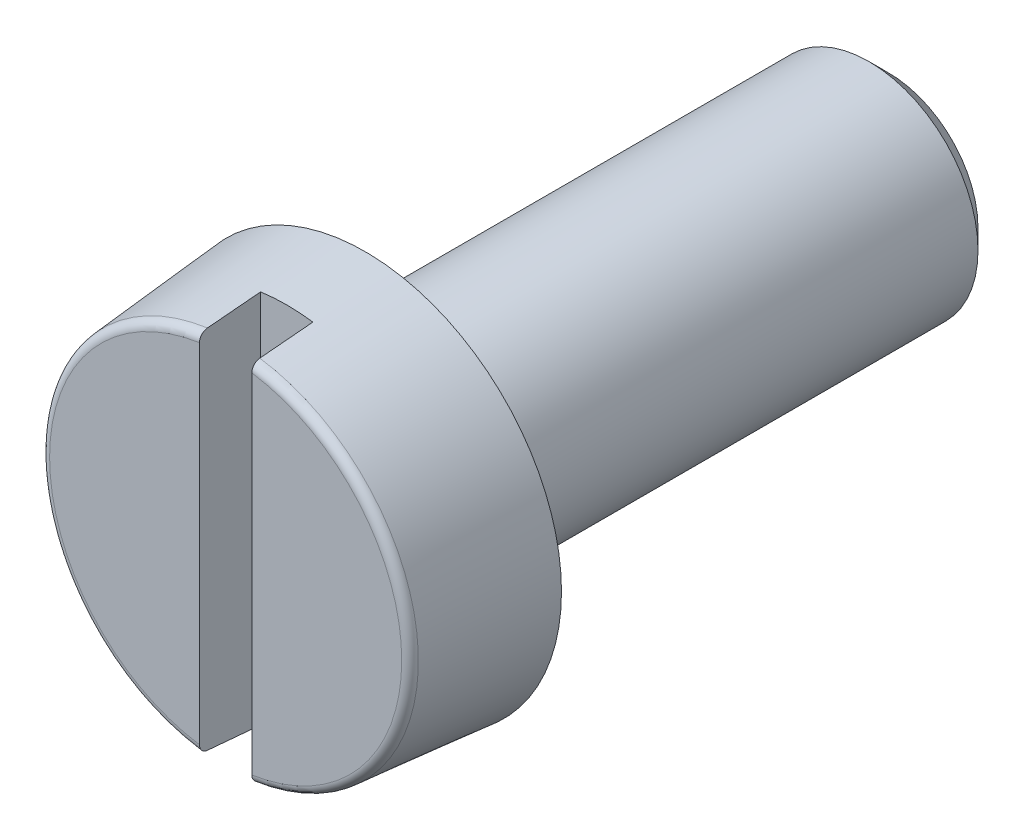
SolidWorks part; units mm, degrees
ref_plane "Front Plane" through (0, 0, 0) normal (0, 0, 1) x (1, 0, 0)
ref_plane "Top Plane" through (0, 0, 0) normal (0, 1, 0) x (1, 0, 0)
ref_plane "Right Plane" through (0, 0, 0) normal (1, 0, 0) x (0, 0, -1)
sketch "Sketch1" plane through (0, 0, 0) normal (1, 0, 0) x (0, 0, -1)
  line L0 (0, 0) -> (18.1531, 0) construction
  line L3 (0, 0) -> (0, 2.0184)
  line L4 (0.0913, 2.118) -> (1.6, 2.25)
  line L5 (1.6, 2.25) -> (1.6, 1.35)
  line L6 (1.7, 1.25) -> (7.375, 1.25)
  line L7 (7.375, 1.25) -> (7.6, 1.025)
  line L8 (7.6, 1.025) -> (7.6, 0)
  line L9 (7.6, 0) -> (0, 0)
  arc A0 (0, 2.0184) -> (0.0913, 2.118) centre (0.1, 2.0184) cw
  arc A1 (1.6, 1.35) -> (1.7, 1.25) centre (1.7, 1.35) ccw
  dimension "a" = 0.1
  dimension "R" = 0.1
  dimension "D1" = 45
  dimension "Dk" = 4.5
  dimension "K" = 1.6
  dimension "Hole1" = 2.5
  dimension "Hole2" = 2.05
  dimension "Length" = 6
  dimension "D8" = 85
revolve "Revolve1" add sketch "Sketch1" angle 360 about L0
cosmetic thread "Cosmetic Thread1" parameters "D1"=5.1, "D2"=2.5
sketch "Sketch2" plane through (0, 0, 0) normal (0, 0, 1) x (1, 0, 0)
  line L0 (0, 0) -> (0, 2.25) construction
  line L1 (-0.3, 2.25) -> (0.3, 2.25)
  line L2 (0.3, 2.25) -> (0.3, -2.25)
  line L3 (-0.3, 2.25) -> (-0.3, -2.25)
  line L4 (0, 0) -> (-2.25, 0) construction
  line L5 (-0.3, -2.25) -> (0.3, -2.25)
  circle A0 centre (0, 0) radius 2.25 construction
  point P8 (-0.3, 0)
  point P13 (0.3, 0)
  dimension "N" = 0.6
extrude "Cut-Extrude1" cut sketch "Sketch2" against normal blind 0.7
